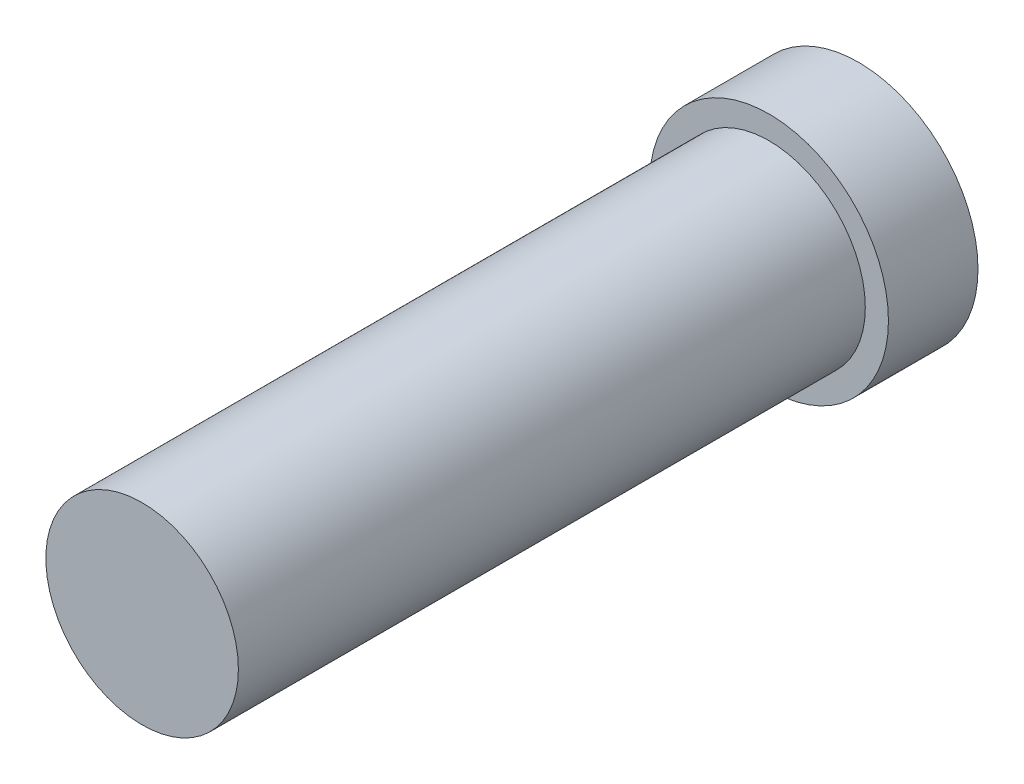
SolidWorks part; units mm, degrees
ref_plane "Front Plane" through (0, 0, 0) normal (0, 0, 1) x (1, 0, 0)
ref_plane "Top Plane" through (0, 0, 0) normal (0, 1, 0) x (1, 0, 0)
ref_plane "Right Plane" through (0, 0, 0) normal (1, 0, 0) x (0, 0, -1)
sketch "Sketch1" plane through (0, 0, 0) normal (0, 0, 1) x (1, 0, 0)
  circle A0 centre (0, 0) radius 3.225
  dimension "D1" = 6.45
extrude "Boss-Extrude1" add sketch "Sketch1" along normal blind 21 contours A0
sketch "Sketch2" plane through (0, 0, 0) normal (0, 0, 1) x (1, 0, 0)
  circle A0 centre (0, 0) radius 4
  dimension "D1" = 8
extrude "Boss-Extrude2" add sketch "Sketch2" against normal blind 3
